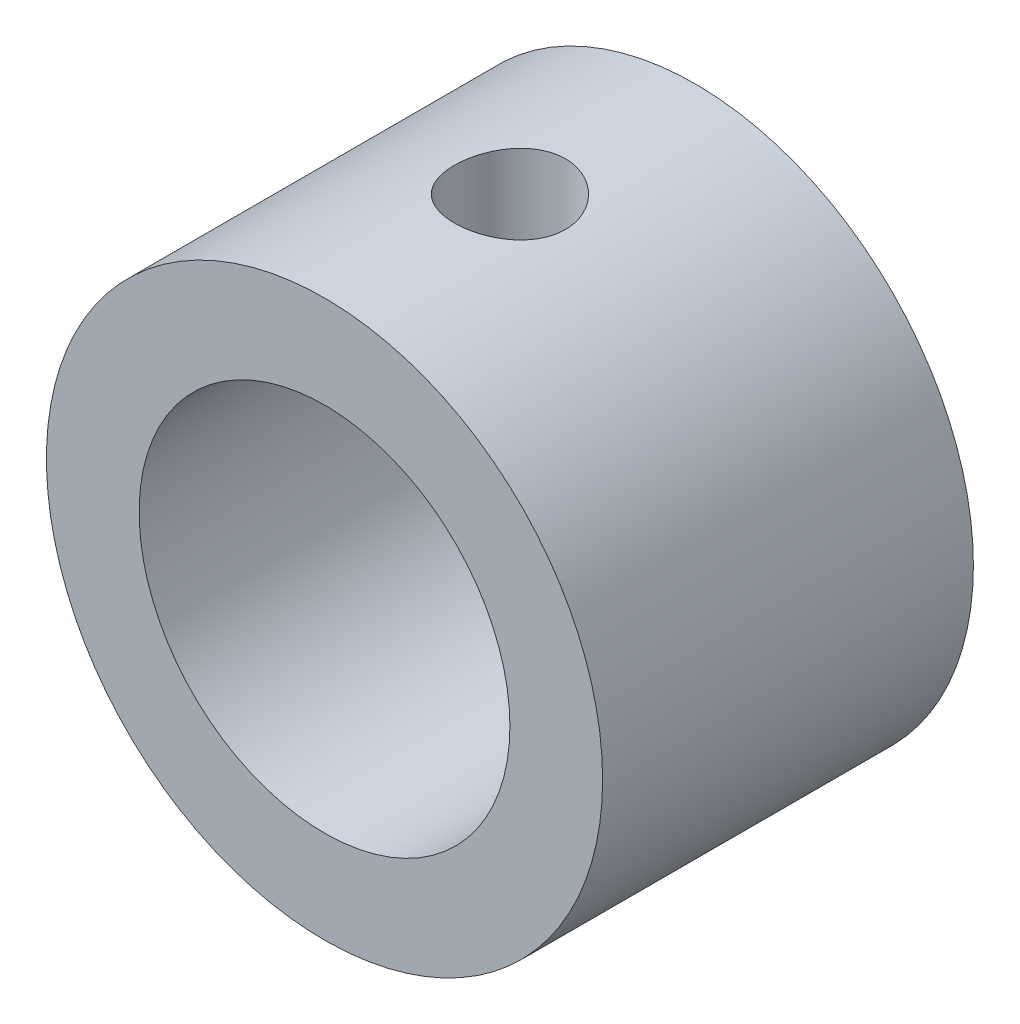
SolidWorks part; units mm, degrees
ref_plane "Front Plane" through (0, 0, 0) normal (0, 0, 1) x (1, 0, 0)
ref_plane "Top Plane" through (0, 0, 0) normal (0, 1, 0) x (1, 0, 0)
ref_plane "Right Plane" through (0, 0, 0) normal (1, 0, 0) x (0, 0, -1)
sketch "Sketch1" plane through (0, 0, 0) normal (0, 0, 1) x (1, 0, 0)
  circle A0 centre (0, 0) radius 7.5
  circle A1 centre (0, 0) radius 5
  dimension "D1" = 10
  dimension "D2" = 15
extrude "Boss-Extrude1" add sketch "Sketch1" along normal mid plane 10
sketch "Sketch2" plane through (0, 0, 0) normal (0, 1, 0) x (1, 0, 0)
  circle A0 centre (0, 0) radius 1.5
  dimension "D1" = 3
extrude "Cut-Extrude1" cut sketch "Sketch2" along normal blind 9 contours A0
